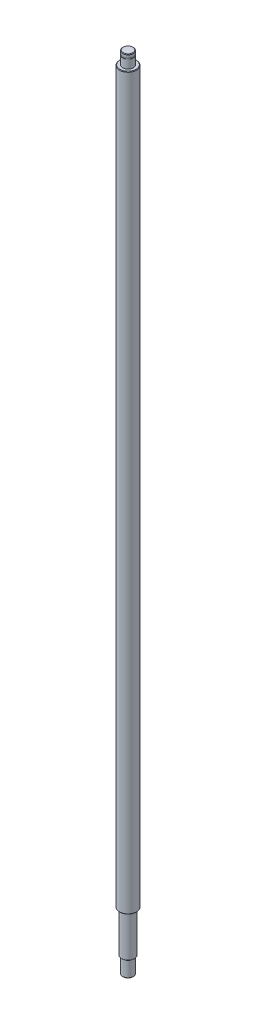
SolidWorks part; units mm, degrees
material "Сталь 40 ГОСТ 535-88"
ref_plane "Спереди" through (0, 0, 0) normal (0, 0, 1) x (1, 0, 0)
ref_plane "Сверху" through (0, 0, 0) normal (0, 1, 0) x (1, 0, 0)
ref_plane "Справа" through (0, 0, 0) normal (1, 0, 0) x (0, 0, -1)
sketch "Эскиз1" plane through (0, 0, 0) normal (0, 0, 1) x (1, 0, 0)
  line L0 (0, 0) -> (-5, 0)
  line L1 (-5, 0) -> (-5, 15)
  line L2 (-5, 15) -> (-6, 15)
  line L3 (-5, 738) -> (-5, 746)
  line L4 (-5, 746) -> (-4.8, 746)
  line L5 (-6, 15) -> (-6, 54)
  line L6 (-6, 54) -> (-8, 54)
  line L7 (-8, 54) -> (-8, 738)
  line L8 (-8, 738) -> (-5, 738)
  line L9 (-4.8, 746) -> (-4.8, 747.15)
  line L10 (-5, 750) -> (0, 750)
  line L11 (0, 750) -> (0, 0) construction
  line L12 (0, 0) -> (0, 750)
  line L13 (-4.8, 747.15) -> (-5, 747.15)
  line L14 (-5, 747.15) -> (-5, 750)
  line L15 (0, 750) -> (0, 365.7796) construction
  dimension "D1" = 10
  dimension "D2" = 15
  dimension "D5" = 12
  dimension "D6" = 39
  dimension "D7" = 16
  dimension "D10" = 12
  dimension "D3" = 750
  dimension "D4" = 10
  dimension "D8" = 8
  dimension "D9" = 1.15
  dimension "D11" = 9.6
revolve "Повернуть1" add sketch "Эскиз1" angle 360 about L11
cosmetic thread "Условное изображение резьбы1"
chamfer "Фаска1" distance 0.5 angle 45 5 edges at (-5, 0, 0) (-8, 54, 0) (-8, 738, 0) (-6, 15, 0) (-5, 750, 0)
equation "\"D3@Эскиз1\"   = 750"
